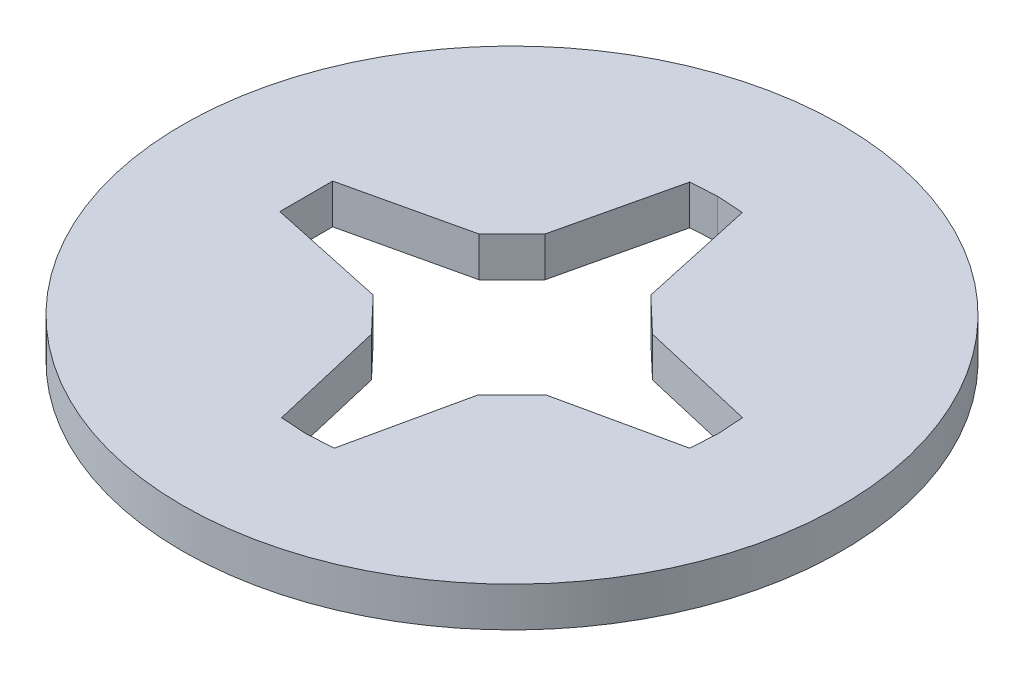
SolidWorks part; units mm, degrees
ref_plane "Front Plane" through (0, 0, 0) normal (0, 0, 1) x (1, 0, 0)
ref_plane "Top Plane" through (0, 0, 0) normal (0, 1, 0) x (1, 0, 0)
ref_plane "Right Plane" through (0, 0, 0) normal (1, 0, 0) x (0, 0, -1)
sketch "Sketch1" plane through (0, 0, 0) normal (0, 1, 0) x (1, 0, 0)
  line L0 (-15.5, -0.0664) -> (-15.5, 1.9336)
  line L9 (0.0664, 15.5) -> (2.0585, 15.372)
  line L18 (6.6328, -4) -> (4, -6.6328)
  line L19 (-4, -6.6328) -> (-6.5, -4)
  line L20 (-6.5, 4) -> (-4, 6.5)
  line L21 (4, 6.5) -> (6.6328, 4)
  line L23 (2.0585, 15.372) -> (4, 6.5)
  line L24 (0.0664, 15.5) -> (-1.9295, 15.3715)
  line L25 (-1.9295, 15.3715) -> (-4, 6.5)
  line L26 (0.0664, -15.6328) -> (2.0623, -15.5043)
  line L27 (-15.5, -0.0664) -> (-15.5, -2.0664)
  line L28 (-15.5, -2.0664) -> (-6.5, -4)
  line L29 (-15.5, 1.9336) -> (-6.5, 4)
  line L30 (0.0664, -15.6328) -> (-1.9295, -15.5043)
  line L31 (-4, -6.6328) -> (-1.9295, -15.5043)
  line L32 (4, -6.6328) -> (2.0623, -15.5043)
  line L33 (15.6328, -0.0664) -> (15.5038, -2.0664)
  line L34 (15.6328, -0.0664) -> (15.5038, 1.9336)
  line L35 (6.6328, 4) -> (15.5038, 1.9336)
  line L36 (6.6328, -4) -> (15.5038, -2.0664)
  circle A0 centre (0.0664, -0.0664) radius 24.9336
extrude "Boss-Extrude1" add sketch "Sketch1" along normal blind 3
